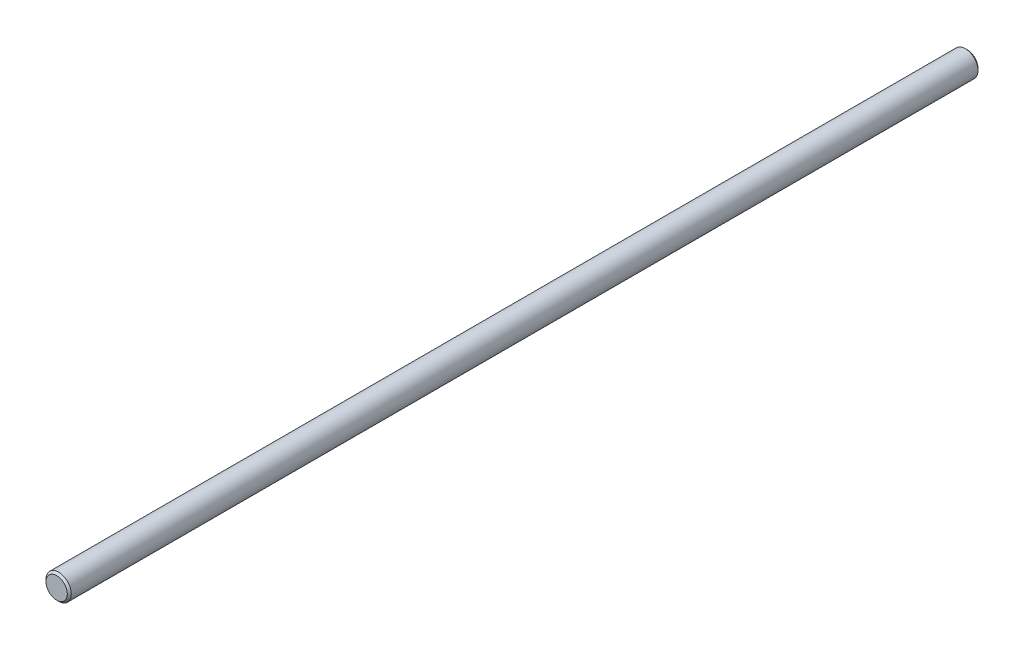
SolidWorks part; units mm, degrees
material "Chrome Stainless Steel"
ref_plane "Front Plane" through (0, 0, 0) normal (0, 0, 1) x (1, 0, 0)
ref_plane "Top Plane" through (0, 0, 0) normal (0, 1, 0) x (1, 0, 0)
ref_plane "Right Plane" through (0, 0, 0) normal (1, 0, 0) x (0, 0, -1)
sketch "Sketch1" plane through (0, 0, 0) normal (0, 0, 1) x (1, 0, 0)
  circle A0 centre (0, 0) radius 3.175
  dimension "D1" = 6.35
extrude "Boss-Extrude1" add sketch "Sketch1" along normal blind 228.6
chamfer "Chamfer1" distance 0.5 angle 45 2 edges at (3.175, 0, 0) (3.175, 0, 228.6)
